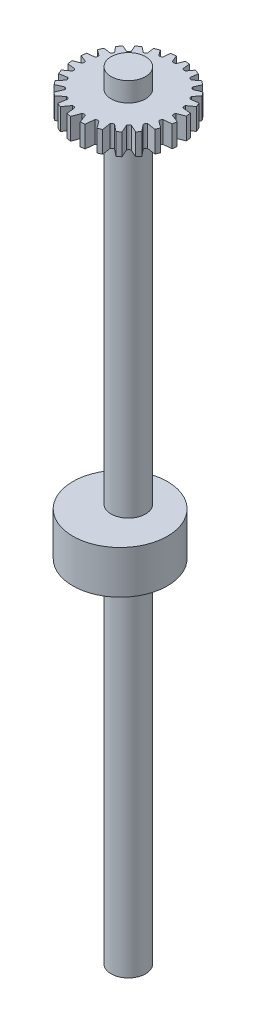
SolidWorks part; units mm, degrees
ref_plane "Alzado" through (0, 0, 0) normal (0, 0, 1) x (1, 0, 0)
ref_plane "Planta" through (0, 0, 0) normal (0, 1, 0) x (1, 0, 0)
ref_plane "Vista lateral" through (0, 0, 0) normal (1, 0, 0) x (0, 0, -1)
sketch "Croquis1" plane through (0, 0, 0) normal (0, 1, 0) x (1, 0, 0)
  circle A0 centre (0, 0) radius 4
  dimension "D1" = 8
extrude "Saliente-Extruir1" add sketch "Croquis1" along normal blind 171
sketch "Croquis3" plane through (0, 171, 0) normal (0, 1, 0) x (1, 0, 0)
  line L0 (0, 10.5439) -> (0, 9.4746) construction
  line L1 (1.0507, 12.2165) -> (0.4728, 10.715)
  line L2 (-1.0507, 12.2165) -> (-0.4728, 10.715)
  line L3 (3.9887, 11.5947) -> (3.0142, 10.2559)
  line L4 (2.0886, 12.0824) -> (2.2608, 10.4578)
  line L5 (6.8331, 10.1811) -> (5.5103, 9.1118)
  line L6 (5.0948, 11.153) -> (4.8348, 9.5018)
  line L7 (9.2289, 8.0731) -> (7.6251, 7.3607)
  line L8 (7.7718, 9.484) -> (7.0736, 7.9122)
  line L9 (11.0065, 5.404) -> (9.2147, 5.1219)
  line L10 (9.9409, 7.1781) -> (8.8248, 5.7973)
  line L11 (12.0342, 2.3504) -> (10.1707, 2.5479)
  line L12 (11.4522, 4.381) -> (9.9688, 3.3013)
  line L13 (12.23, -0.8794) -> (10.4279, -0.1858)
  line L14 (12.1952, 1.2744) -> (10.4279, 0.5942)
  line L15 (11.5704, -4.0586) -> (9.9688, -2.8929)
  line L16 (12.1081, -1.9341) -> (10.1707, -2.1395)
  line L17 (10.0948, -6.9601) -> (8.8248, -5.3889)
  line L18 (11.1852, -5.0238) -> (9.2147, -4.7135)
  line L19 (7.9043, -9.3739) -> (7.0736, -7.5038)
  line L20 (9.4803, -7.7763) -> (7.6251, -6.9523)
  line L21 (5.1548, -11.1254) -> (4.8348, -9.0934)
  line L22 (7.1055, -9.9929) -> (5.5103, -8.7034)
  line L23 (2.0445, -12.09) -> (2.2608, -10.0494)
  line L24 (4.2249, -11.5108) -> (3.0142, -9.8475)
  line L25 (-1.2025, -12.2025) -> (-0.4728, -10.3066)
  line L26 (1.0425, -12.2172) -> (0.3071, -10.3066)
  line L27 (-4.3552, -11.4621) -> (-3.1799, -9.8475)
  line L28 (-2.2134, -12.0602) -> (-2.4266, -10.0494)
  line L29 (-7.1933, -9.9299) -> (-5.676, -8.7034)
  line L30 (-5.3091, -11.0526) -> (-5.0005, -9.0934)
  line L31 (-9.5244, -7.7223) -> (-7.7909, -6.9523)
  line L32 (-8.0244, -9.2712) -> (-7.2394, -7.5038)
  line L33 (-11.1961, -4.9994) -> (-9.3805, -4.7135)
  line L34 (-10.1706, -6.8488) -> (-8.9905, -5.3889)
  line L35 (-12.1052, -1.952) -> (-10.3364, -2.1395)
  line L36 (-11.6038, -3.9623) -> (-10.1346, -2.8929)
  line L37 (-12.2015, 1.213) -> (-10.5937, 0.5942)
  line L38 (-12.2343, -0.8172) -> (-10.5937, -0.1858)
  line L39 (-11.488, 4.2864) -> (-10.1346, 3.3013)
  line L40 (-12.0307, 2.3683) -> (-10.3364, 2.5479)
  line L41 (-10.0186, 7.0693) -> (-8.9905, 5.7973)
  line L42 (-11.0184, 5.3798) -> (-9.3805, 5.1219)
  line L43 (-7.8929, 9.3835) -> (-7.2394, 7.9122)
  line L44 (-9.2751, 8.02) -> (-7.7909, 7.3607)
  line L45 (-5.2492, 11.0812) -> (-5.0005, 9.5018)
  line L46 (-6.9233, 10.12) -> (-5.676, 9.1118)
  line L47 (-2.2576, 12.052) -> (-2.4266, 10.4578)
  line L48 (-4.1208, 11.5484) -> (-3.1799, 10.2559)
  arc A0 (-4.1208, 11.5484) -> (-5.2492, 11.0812) centre (0, 0) ccw
  arc A1 (0.4728, 10.715) -> (-0.4728, 10.715) centre (0, 11.2827) cw
  arc A2 (3.0142, 10.2559) -> (2.2608, 10.4578) centre (2.7845, 10.9052) cw
  arc A3 (5.5103, 9.1118) -> (4.8348, 9.5018) centre (5.4564, 9.7985) cw
  arc A4 (7.6251, 7.3607) -> (7.0736, 7.9122) centre (7.7508, 8.0379) cw
  arc A5 (9.2147, 5.1219) -> (8.8248, 5.7973) centre (9.5114, 5.7435) cw
  arc A6 (10.1707, 2.5479) -> (9.9688, 3.3013) centre (10.6182, 3.0715) cw
  arc A7 (10.4279, -0.1858) -> (10.4279, 0.5942) centre (10.9957, 0.2042) cw
  arc A8 (9.9688, -2.8929) -> (10.1707, -2.1395) centre (10.6182, -2.6631) cw
  arc A9 (8.8248, -5.3889) -> (9.2147, -4.7135) centre (9.5114, -5.3351) cw
  arc A10 (7.0736, -7.5038) -> (7.6251, -6.9523) centre (7.7508, -7.6295) cw
  arc A11 (4.8348, -9.0934) -> (5.5103, -8.7034) centre (5.4564, -9.3901) cw
  arc A12 (2.2608, -10.0494) -> (3.0142, -9.8475) centre (2.7845, -10.4968) cw
  arc A13 (-0.4728, -10.3066) -> (0.3071, -10.3066) centre (-0.0829, -10.8743) cw
  arc A14 (-3.1799, -9.8475) -> (-2.4266, -10.0494) centre (-2.9502, -10.4968) cw
  arc A15 (-5.676, -8.7034) -> (-5.0005, -9.0934) centre (-5.6221, -9.3901) cw
  arc A16 (-7.7909, -6.9523) -> (-7.2394, -7.5038) centre (-7.9166, -7.6295) cw
  arc A17 (-9.3805, -4.7135) -> (-8.9905, -5.3889) centre (-9.6772, -5.3351) cw
  arc A18 (-10.3364, -2.1395) -> (-10.1346, -2.8929) centre (-10.7839, -2.6631) cw
  arc A19 (-10.5937, 0.5942) -> (-10.5937, -0.1858) centre (-11.1614, 0.2042) cw
  arc A20 (-10.1346, 3.3013) -> (-10.3364, 2.5479) centre (-10.7839, 3.0715) cw
  arc A21 (-8.9905, 5.7973) -> (-9.3805, 5.1219) centre (-9.6772, 5.7435) cw
  arc A22 (-7.2394, 7.9122) -> (-7.7909, 7.3607) centre (-7.9166, 8.0379) cw
  arc A23 (-5.0005, 9.5018) -> (-5.676, 9.1118) centre (-5.6221, 9.7985) cw
  arc A24 (-2.4266, 10.4578) -> (-3.1799, 10.2559) centre (-2.9502, 10.9052) cw
  arc A25 (-6.9233, 10.12) -> (-7.8929, 9.3835) centre (0, 0) ccw
  arc A26 (-9.2751, 8.02) -> (-10.0186, 7.0693) centre (0, 0) ccw
  arc A27 (-11.0184, 5.3798) -> (-11.488, 4.2864) centre (0, 0) ccw
  arc A28 (-12.0307, 2.3683) -> (-12.2015, 1.213) centre (0, 0) ccw
  arc A29 (-1.0507, 12.2165) -> (-2.2576, 12.052) centre (0, 0) ccw
  arc A30 (2.0886, 12.0824) -> (1.0507, 12.2165) centre (0, 0) ccw
  arc A31 (5.0948, 11.153) -> (3.9887, 11.5947) centre (0, 0) ccw
  arc A32 (7.7718, 9.484) -> (6.8331, 10.1811) centre (0, 0) ccw
  arc A33 (9.9409, 7.1781) -> (9.2289, 8.0731) centre (0, 0) ccw
  arc A34 (11.4522, 4.381) -> (11.0065, 5.404) centre (0, 0) ccw
  arc A35 (12.1952, 1.2744) -> (12.0342, 2.3504) centre (0, 0) ccw
  arc A36 (12.1081, -1.9341) -> (12.23, -0.8794) centre (0, 0) ccw
  arc A37 (11.1852, -5.0238) -> (11.5704, -4.0586) centre (0, 0) ccw
  arc A38 (9.4803, -7.7763) -> (10.0948, -6.9601) centre (0, 0) ccw
  arc A39 (7.1055, -9.9929) -> (7.9043, -9.3739) centre (0, 0) ccw
  arc A40 (4.2249, -11.5108) -> (5.1548, -11.1254) centre (0, 0) ccw
  arc A41 (1.0425, -12.2172) -> (2.0445, -12.09) centre (0, 0) ccw
  arc A42 (-2.2134, -12.0602) -> (-1.2025, -12.2025) centre (0, 0) ccw
  arc A43 (-5.3091, -11.0526) -> (-4.3552, -11.4621) centre (0, 0) ccw
  arc A44 (-8.0244, -9.2712) -> (-7.1933, -9.9299) centre (0, 0) ccw
  arc A45 (-10.1706, -6.8488) -> (-9.5244, -7.7223) centre (0, 0) ccw
  arc A46 (-11.6038, -3.9623) -> (-11.1961, -4.9994) centre (0, 0) ccw
  arc A47 (-12.2343, -0.8172) -> (-12.1052, -1.952) centre (0, 0) ccw
  point P123 (0, 0)
extrude "Saliente-Extruir3" add sketch "Croquis3" along normal blind 5
sketch "Croquis4" plane through (0, 176, 0) normal (0, 1, 0) x (1, 0, 0)
  circle A0 centre (0, 0) radius 4
  dimension "D1" = 8
extrude "Saliente-Extruir4" add sketch "Croquis4" along normal blind 4.5
ref_plane "Plano1" through (0, 85.5, 0) normal (0, -1, 0) x (-1, 0, 0)
sketch "Croquis5" plane through (0, 85.5, 0) normal (0, -1, 0) x (-1, 0, 0)
  circle A1 centre (0, -1.9124) radius 11
  dimension "D1" = 22
  dimension "D2" = 1.9124
extrude "Saliente-Extruir5" add sketch "Croquis5" against normal blind 7 and the other way blind 3 separate body
